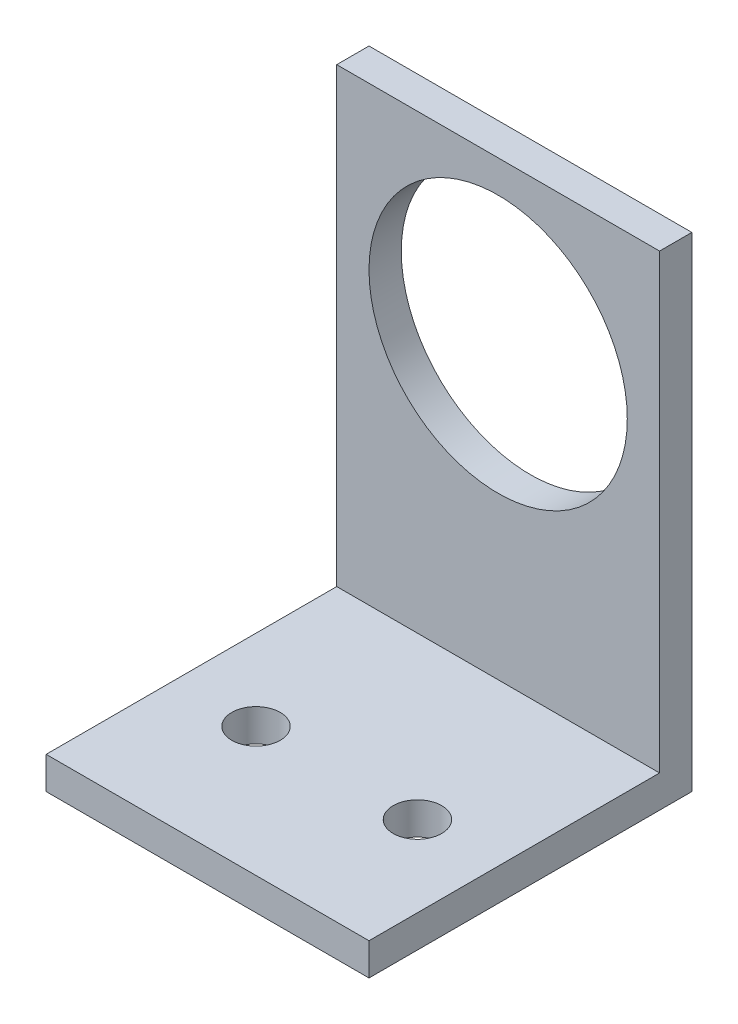
SolidWorks part; units mm, degrees
ref_plane "前视基准面" through (0, 0, 0) normal (0, 0, 1) x (1, 0, 0)
ref_plane "上视基准面" through (0, 0, 0) normal (0, 1, 0) x (1, 0, 0)
ref_plane "右视基准面" through (0, 0, 0) normal (1, 0, 0) x (0, 0, -1)
sketch "草图1" plane through (0, 0, 0) normal (0, 0, 1) x (1, 0, 0)
  line L1 (-10, 19) -> (10, 19)
  line L2 (-10, 19) -> (-10, -19)
  line L3 (-10, -19) -> (10, -19)
  line L4 (10, 19) -> (10, -19)
  line L5 (-10, 19) -> (10, -19) construction
  line L6 (-10, -19) -> (10, 19) construction
  point P0 (0, 0)
  dimension "D1" = 20
  dimension "D2" = 38
extrude "凸台-拉伸1" add sketch "草图1" along normal blind 3
sketch "草图2" plane through (0, 0, 3) normal (0, 0, 1) x (1, 0, 0)
  line L0 (10, -19) -> (10, 19) construction
  line L1 (-10, -19) -> (10, -19)
  line L2 (-10, -19) -> (-10, -16)
  line L3 (-10, -16) -> (10, -16)
  line L4 (10, -19) -> (10, -16)
  dimension "D1" = 3
extrude "凸台-拉伸2" add sketch "草图2" along normal blind 35
sketch "草图4" plane through (0, -16, 0) normal (0, 1, 0) x (1, 0, 0)
  line L0 (-10, -38) -> (-10, -3) construction
  line L1 (10, -38) -> (10, -3) construction
  line L2 (10, -38) -> (-10, -38) construction
  circle A0 centre (-5, -13) radius 1.5
  circle A1 centre (5, -13) radius 1.5
  dimension "D1" = 5
  dimension "D2" = 5
  dimension "D3" = 3
  dimension "D4" = 3
  dimension "D5" = 25
  dimension "D6" = 25
extrude "切除-拉伸2" cut sketch "草图4" against normal blind 10
sketch "草图6" plane through (0, 0, 0) normal (0, 0, -1) x (-1, 0, 0)
  line L0 (10, -19) -> (-10, -19) construction
  circle A0 centre (0, 1) radius 8
  dimension "D1" = 16
  dimension "D2" = 20
extrude "切除-拉伸4" cut sketch "草图6" against normal blind 10
sketch "草图7" plane through (0, 0, 38) normal (0, 0, 1) x (1, 0, 0)
  line L1 (16.8681, -12.8016) -> (-31.8347, -12.8016)
  line L2 (16.8681, -12.8016) -> (16.8681, -27.8272)
  line L3 (16.8681, -27.8272) -> (-31.8347, -27.8272)
  line L4 (-31.8347, -12.8016) -> (-31.8347, -27.8272)
extrude "切除-拉伸5" cut sketch "草图7" against normal blind 17
sketch "草图8" plane through (0, 19, 0) normal (0, 1, 0) x (1, 0, 0)
  line L1 (11.7038, 2.6153) -> (-12.067, 2.6153)
  line L2 (11.7038, 2.6153) -> (11.7038, -5.2498)
  line L3 (11.7038, -5.2498) -> (-12.067, -5.2498)
  line L4 (-12.067, 2.6153) -> (-12.067, -5.2498)
extrude "切除-拉伸6" cut sketch "草图8" against normal blind 8
sketch "草图9" plane through (0, -16, 0) normal (0, 1, 0) x (1, 0, 0)
  line L1 (-10, -3) -> (15.8519, -3)
  line L2 (-10, -3) -> (-10, -22.3701)
  line L3 (-10, -22.3701) -> (15.8519, -22.3701)
  line L4 (15.8519, -3) -> (15.8519, -22.3701)
extrude "切除-拉伸7" cut sketch "草图9" against normal blind 1
sketch "草图10" plane through (0, 0, 0) normal (0, 0, -1) x (-1, 0, 0)
  line L1 (31.3723, -25.1266) -> (-31.2951, -25.1266)
  line L2 (31.3723, -25.1266) -> (31.3723, 18.3373)
  line L3 (31.3723, 18.3373) -> (-31.2951, 18.3373)
  line L4 (-31.2951, -25.1266) -> (-31.2951, 18.3373)
extrude "切除-拉伸8" cut sketch "草图10" against normal blind 1
